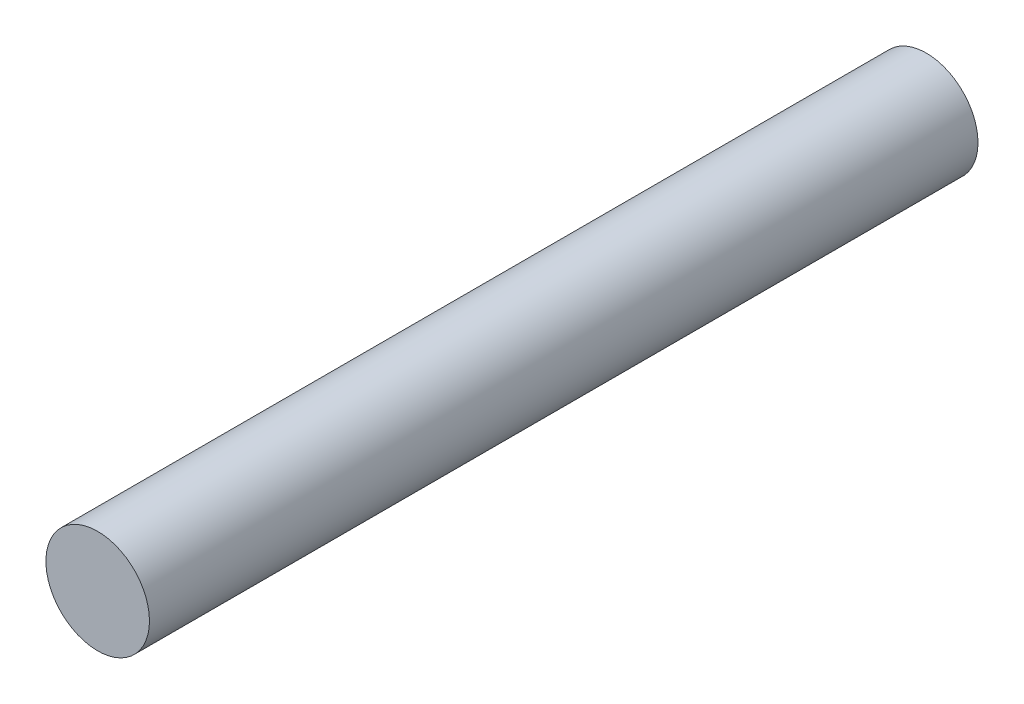
SolidWorks part; units mm, degrees
ref_plane "Front" through (0, 0, 0) normal (0, 0, 1) x (1, 0, 0)
ref_plane "Top" through (0, 0, 0) normal (0, 1, 0) x (1, 0, 0)
ref_plane "Right" through (0, 0, 0) normal (1, 0, 0) x (0, 0, -1)
sketch "Sketch1" plane through (0, 0, 0) normal (0, 0, 1) x (1, 0, 0)
  circle A0 centre (0, 0) radius 6.35
  dimension "D1" = 12.7
extrude "Boss-Extrude1" add sketch "Sketch1" along normal blind 101.6
